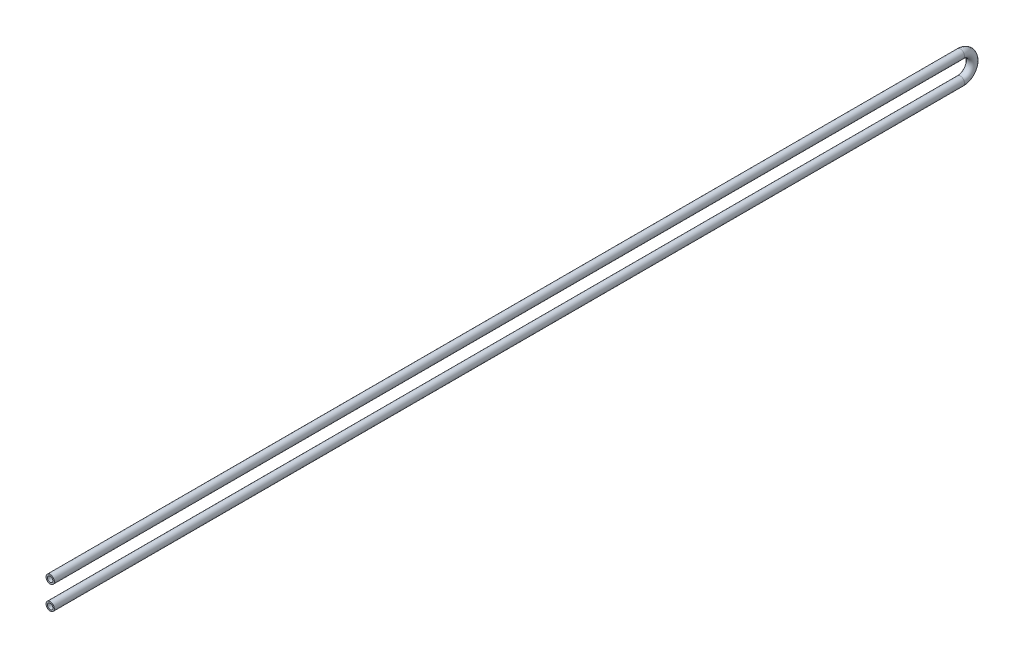
SolidWorks part; units mm, degrees
material "AISI 304"
ref_plane "Front Plane" through (0, 0, 0) normal (0, 0, 1) x (1, 0, 0)
ref_plane "Top Plane" through (0, 0, 0) normal (0, 1, 0) x (1, 0, 0)
ref_plane "Right Plane" through (0, 0, 0) normal (1, 0, 0) x (0, 0, -1)
sketch "Sketch1" plane through (0, 0, 0) normal (1, 0, 0) x (0, 0, -1)
  line L0 (0, 0) -> (0, 30) construction
  line L1 (0, 30) -> (2325, 30)
  line L2 (2325, -30) -> (0, -30)
  arc A0 (2325, 30) -> (2325, -30) centre (2325, 0) cw
  dimension "D1" = 30
  dimension "D2" = 2325
sketch "Sketch2" plane through (0, 0, 0) normal (0, 0, 1) x (1, 0, 0)
  circle A0 centre (0, 30) radius 10.65
  circle A2 centre (0, 30) radius 6.92
  dimension "D1" = 13.84
  dimension "D2" = 21.3
sweep "Sweep1" add profiles "Sketch2" path "Sketch1"
